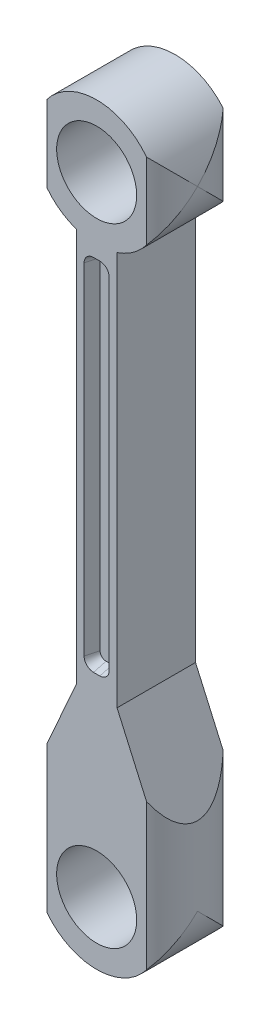
SolidWorks part; units mm, degrees
ref_plane "Front Plane" through (0, 0, 0) normal (0, 0, 1) x (1, 0, 0)
ref_plane "Top Plane" through (0, 0, 0) normal (0, 1, 0) x (1, 0, 0)
ref_plane "Right Plane" through (0, 0, 0) normal (1, 0, 0) x (0, 0, -1)
sketch "Sketch1" plane through (0, 0, 0) normal (0, 0, 1) x (1, 0, 0)
  line L0 (-10.16, 0) -> (-10.16, 12.7)
  line L1 (-10.16, 12.7) -> (-3.302, 28.176)
  line L2 (-3.302, 28.176) -> (-3.302, 91.9915)
  line L3 (10.16, 0) -> (10.16, 12.7)
  line L4 (10.16, 12.7) -> (3.302, 28.176)
  line L5 (3.302, 28.176) -> (3.302, 91.9915)
  line L6 (10.16, 11.5927) -> (10.16, 31.5923) construction
  line L7 (-10.16, 10.1069) -> (-10.16, 31.0928) construction
  circle A0 centre (0, 0) radius 6.477
  circle A1 centre (0, 101.6) radius 6.477
  arc A2 (3.302, 91.9915) -> (-3.302, 91.9915) centre (0, 101.6) ccw
  arc A3 (-10.16, 0) -> (10.16, 0) centre (0, 0) ccw
  dimension "D2" = 12.954
  dimension "D3" = 12.954
  dimension "D4" = 20.32
  dimension "D5" = 20.32
  dimension "D1" = 101.6
  dimension "D6" = 12.7
  dimension "D7" = 6.604
  dimension "D8" = 23.9
  dimension "D9" = 23.9
extrude "Boss-Extrude2" add sketch "Sketch1" against normal blind 12.7
sketch "Sketch3" plane through (0, 0, 0) normal (0, 0, 1) x (1, 0, 0)
  line L0 (3.302, 28.176) -> (3.302, 91.9915) construction
  line L1 (-0.508, 89.408) -> (0.508, 89.408)
  line L2 (-2.032, 87.884) -> (-2.032, 32.766)
  line L3 (-0.508, 31.242) -> (0.508, 31.242)
  line L4 (2.032, 87.884) -> (2.032, 32.766)
  line L5 (-3.302, 91.9915) -> (-3.302, 28.176) construction
  circle A0 centre (0, 0) radius 6.477 construction
  circle A1 centre (0, 101.6) radius 6.477 construction
  arc A2 (0.508, 31.242) -> (2.032, 32.766) centre (0.508, 32.766) ccw
  arc A3 (-2.032, 32.766) -> (-0.508, 31.242) centre (-0.508, 32.766) ccw
  arc A4 (0.508, 89.408) -> (2.032, 87.884) centre (0.508, 87.884) cw
  arc A5 (-0.508, 89.408) -> (-2.032, 87.884) centre (-0.508, 87.884) ccw
  dimension "D1" = 31.242
  dimension "D5" = 1.524
  dimension "D2" = 12.192
  dimension "D3" = 1.27
  dimension "D4" = 1.27
extrude "Cut-Extrude2" cut sketch "Sketch3" against normal blind 2.032 draft 15
ref_plane "Plane3" through (0, 0, -6.35) normal (0, 0, 1) x (1, 0, 0)
mirror "Mirror1" about plane through (0, 0, -6.35) normal (0, 0, 1) of "Cut-Extrude2"
sketch "Sketch4" plane through (0, 0, 0) normal (0, 1, 0) x (1, 0, 0)
  circle A0 centre (0, 6.1688) radius 10.16
  point P2 (0, 0)
  dimension "D1" = 20.32
extrude "Cut-Extrude1" cut sketch "Sketch4" against normal through all both and the other way through all flip side to cut
